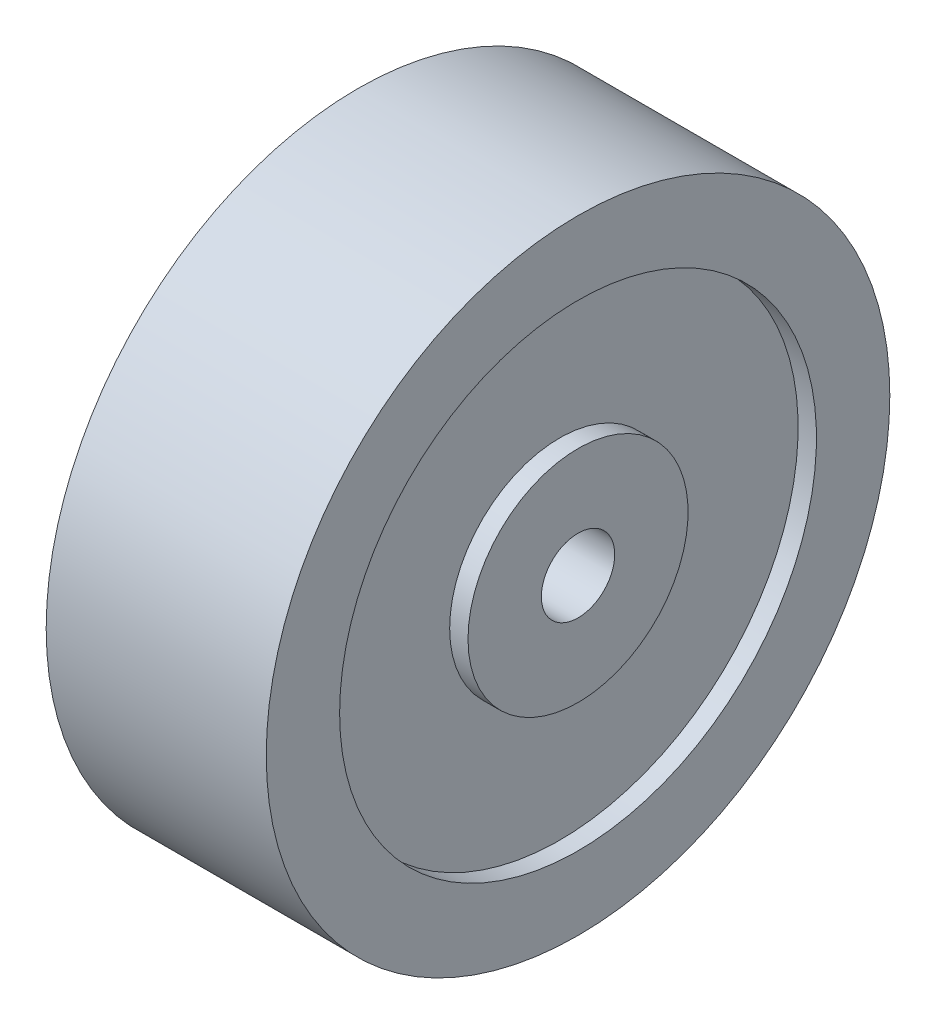
SolidWorks part; units mm, degrees
ref_plane "Alzado" through (0, 0, 0) normal (0, 0, 1) x (1, 0, 0)
ref_plane "Planta" through (0, 0, 0) normal (0, 1, 0) x (1, 0, 0)
ref_plane "Vista lateral" through (0, 0, 0) normal (1, 0, 0) x (0, 0, -1)
sketch "Croquis1" plane through (0, 0, 0) normal (0, 0, 1) x (1, 0, 0)
  line L0 (0, 0) -> (51.1688, 0) construction
  line L2 (0, 6.35) -> (0, 19.05)
  line L3 (0, 6.35) -> (38.1, 6.35)
  line L4 (0, 53.975) -> (38.1, 53.975)
  line L6 (0, 19.05) -> (3.175, 19.05)
  line L7 (3.175, 19.05) -> (3.175, 41.275)
  line L8 (3.175, 41.275) -> (0, 41.275)
  line L9 (0, 41.275) -> (0, 53.975)
  line L10 (38.1, 6.35) -> (38.1, 19.05)
  line L11 (38.1, 19.05) -> (34.925, 19.05)
  line L12 (34.925, 19.05) -> (34.925, 41.275)
  line L13 (34.925, 41.275) -> (38.1, 41.275)
  line L14 (38.1, 41.275) -> (38.1, 53.975)
  dimension "D1" = 6.35
  dimension "D2" = 3.175
  dimension "D3" = 12.7
  dimension "D4" = 12.7
  dimension "D5" = 22.225
  dimension "D6" = 3.175
  dimension "D7" = 3.175
  dimension "D8" = 3.175
  dimension "D9" = 38.1
  dimension "D10" = 12.7
  dimension "D11" = 22.225
revolve "Revolución2" add sketch "Croquis1" angle 360 about L0
